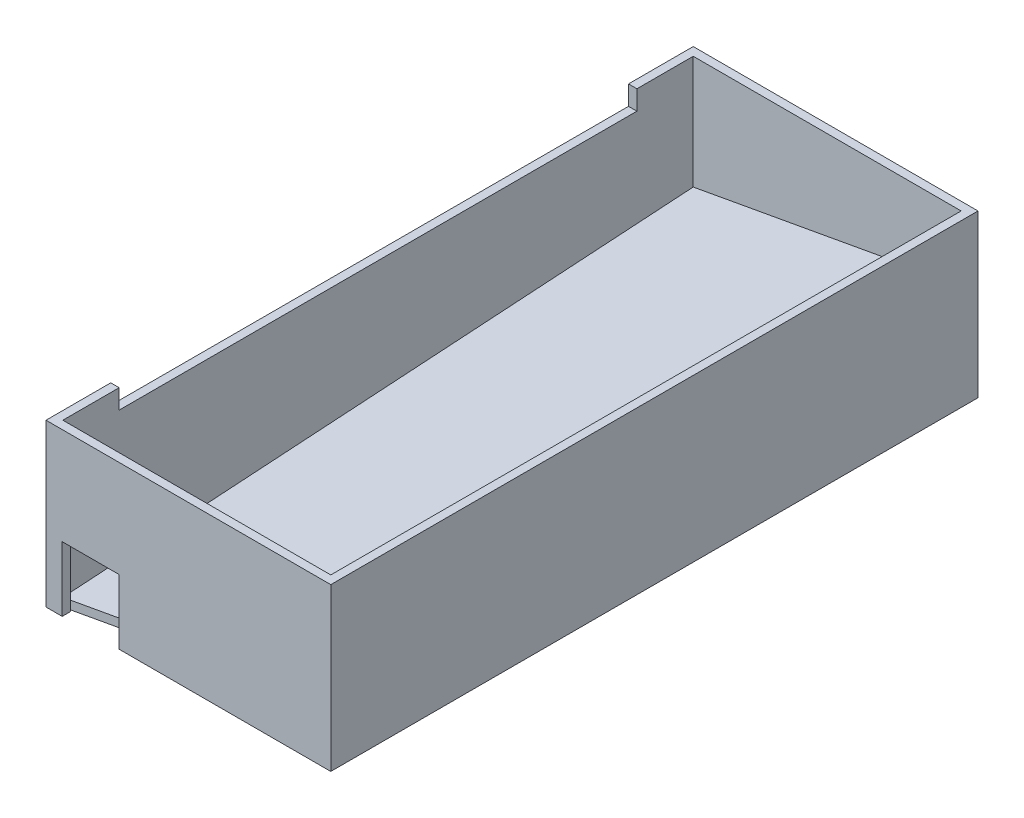
SolidWorks part; units mm, degrees
ref_plane "Front Plane" through (0, 0, 0) normal (0, 0, 1) x (1, 0, 0)
ref_plane "Top Plane" through (0, 0, 0) normal (0, 1, 0) x (1, 0, 0)
ref_plane "Right Plane" through (0, 0, 0) normal (1, 0, 0) x (0, 0, -1)
sketch "Sketch2" plane through (0, 0, 0) normal (0, 1, 0) x (1, 0, 0)
  line L0 (3.302, 3.302) -> (108.458, 3.302)
  line L1 (0, 0) -> (111.76, 0)
  line L2 (0, 0) -> (0, 254)
  line L3 (0, 254) -> (111.76, 254)
  line L4 (111.76, 0) -> (111.76, 254)
  line L5 (108.458, 3.302) -> (108.458, 250.698)
  line L6 (3.302, 250.698) -> (108.458, 250.698)
  line L7 (3.302, 3.302) -> (3.302, 250.698)
  dimension "D2" = 111.76
  dimension "D3" = 254
  dimension "D1" = 3.302
extrude "Boss-Extrude2" add sketch "Sketch2" along normal blind 63.5
sketch "Sketch3" plane through (3.302, 0, 0) normal (1, 0, 0) x (0, 0, -1)
  line L0 (254, 63.5) -> (0, 63.5) construction
  line L1 (228.6, 63.5) -> (25.4, 63.5)
  line L2 (228.6, 63.5) -> (228.6, 55.88)
  line L3 (228.6, 55.88) -> (25.4, 55.88)
  line L4 (25.4, 63.5) -> (25.4, 55.88)
  line L5 (228.6, 55.88) -> (254, 55.88) construction
  line L6 (254, 63.5) -> (254, 0) construction
  line L7 (25.4, 55.88) -> (0, 55.88) construction
  line L8 (0, 63.5) -> (0, 0) construction
  dimension "D1" = 7.62
  dimension "D2" = 25.4
extrude "Cut-Extrude1" cut sketch "Sketch3" against normal blind 63.5
sketch "Sketch4" plane through (0, 0, 0) normal (0, 0, 1) x (1, 0, 0)
  line L0 (0, 0) -> (111.76, 0) construction
  line L1 (6.35, 0) -> (28.702, 0)
  line L2 (6.35, 0) -> (6.35, 25.4)
  line L3 (6.35, 25.4) -> (28.702, 25.4)
  line L4 (28.702, 0) -> (28.702, 25.4)
  line L5 (0, 63.5) -> (0, 0) construction
  dimension "D1" = 6.35
  dimension "D2" = 25.4
  dimension "D3" = 22.352
extrude "Cut-Extrude2" cut sketch "Sketch4" against normal up to next
sketch3d "3DSketch1"
  line L0 (3.302, 3.302, -3.302) -> (108.458, 22.352, -3.302)
  line L1 (3.302, 63.5, -3.302) -> (3.302, 0, -3.302) construction
  line L3 (108.458, 22.352, -3.302) -> (108.458, 38.1, -250.698)
  line L4 (108.458, 63.5, -250.698) -> (108.458, 0, -250.698) construction
  line L5 (108.458, 38.1, -250.698) -> (3.302, 19.05, -250.698)
  line L6 (3.302, 63.5, -250.698) -> (3.302, 0, -250.698) construction
  line L7 (3.302, 19.05, -250.698) -> (3.302, 3.302, -3.302)
  point P4 (0, 0, 0)
  point P12 (3.302, 5.2148, -3.302)
  point P13 (108.458, 31.75, -3.302)
  point P14 (108.458, 31.75, -3.302)
  point P15 (108.458, 31.75, -3.302)
  dimension "D1" = 3.302
  dimension "D2" = 19.05
  dimension "D3" = 38.1
surface "Surface-Fill1" sketch "3DSketch1"
surface "Surface-Extrude1" parameters "D1"=3.302
